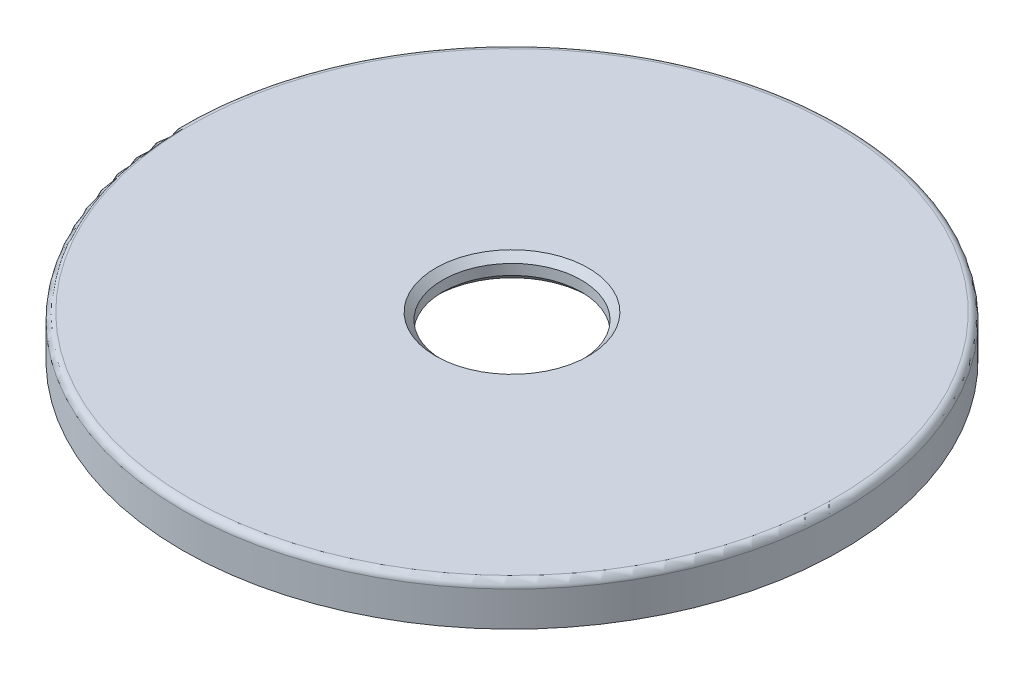
SolidWorks part; units mm, degrees
ref_plane "Front Plane" through (0, 0, 0) normal (0, 0, 1) x (1, 0, 0)
ref_plane "Top Plane" through (0, 0, 0) normal (0, 1, 0) x (1, 0, 0)
ref_plane "Right Plane" through (0, 0, 0) normal (1, 0, 0) x (0, 0, -1)
sketch "Sketch1" plane through (0, 0, 0) normal (0, 1, 0) x (1, 0, 0)
  circle A0 centre (0, 0) radius 47.5
  dimension "D1" = 95
extrude "Boss-Extrude1" add sketch "Sketch1" along normal blind 2
sketch "Sketch2" plane through (0, 0, 0) normal (0, -1, 0) x (1, 0, 0)
  circle A0 centre (0, 0) radius 42.5
  dimension "D1" = 85
extrude "Boss-Extrude2" add sketch "Sketch2" along normal blind 1.5 draft 2
sketch "Sketch5" plane through (0, 2, 0) normal (0, 1, 0) x (1, 0, 0)
  circle A0 centre (0, 0) radius 10
extrude "Cut-Extrude1" cut sketch "Sketch5" against normal blind 4
chamfer "Chamfer1" distance 1 angle 45 2 edges at (0, -1.5, -10) (0, 2, 10)
sketch "Sketch7" plane through (0, 0, 0) normal (0, -1, 0) x (1, 0, 0)
  circle A0 centre (0, 0) radius 47.5
  circle A1 centre (0, 0) radius 45.6
  circle A2 centre (0, 0) radius 42.5 construction
  dimension "D1" = 1.9
  dimension "D2" = 3.1
extrude "Boss-Extrude3" add sketch "Sketch7" along normal blind 4
fillet "Fillet2" radius 1 1 edges at (0, 2, 47.5)
